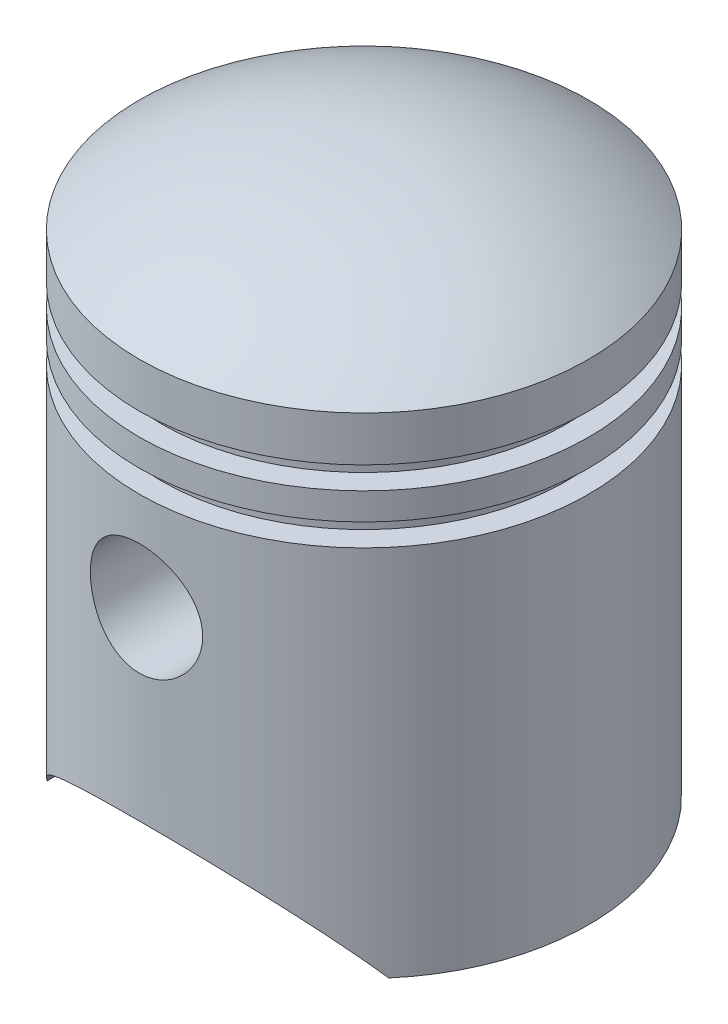
SolidWorks part; units mm, degrees
ref_plane "Front Plane" through (0, 0, 0) normal (0, 0, 1) x (1, 0, 0)
ref_plane "Top Plane" through (0, 0, 0) normal (0, 1, 0) x (1, 0, 0)
ref_plane "Right Plane" through (0, 0, 0) normal (1, 0, 0) x (0, 0, -1)
sketch "Sketch2" plane through (0, 0, 0) normal (0, 0, 1) x (1, 0, 0)
  line L0 (25, 0) -> (25, 41.5)
  line L1 (25, 49.5) -> (22.5, 49.5)
  line L2 (22.5, 49.5) -> (22.5, 47)
  line L3 (22.5, 47) -> (25, 47)
  line L4 (25, 44) -> (22.5, 44)
  line L5 (22.5, 44) -> (22.5, 41.5)
  line L6 (22.5, 41.5) -> (25, 41.5)
  line L7 (25, 49.5) -> (25, 54.5)
  line L8 (25, 44) -> (25, 47)
  line L9 (23, 0) -> (23, 39.5)
  line L10 (20.5, 39.5) -> (23, 39.5)
  line L11 (20.5, 45.5) -> (20.5, 39.5)
  line L12 (20.5, 45.5) -> (20.5, 45.5)
  line L13 (20.5, 45.5) -> (20.5, 45.5)
  line L14 (20.5, 45.5) -> (20.5, 45.5)
  line L15 (20.5, 51.5) -> (20.5, 45.5)
  line L16 (23, 51.5) -> (20.5, 51.5)
  line L17 (23, 51.5) -> (23, 53.4845)
  line L18 (25, 0) -> (23, 0)
  line L19 (0, 62.5) -> (0, 60.4994)
  arc A0 (25, 54.5) -> (0, 62.5) centre (0.9839, 22.5121) ccw
  arc A1 (23, 53.4845) -> (0, 60.4994) centre (0.9839, 22.5121) ccw
  arc A2 (23, 53.4845) -> (0.0492, 60.5006) centre (0.9839, 22.5121) ccw construction
  dimension "D4" = 40
  dimension "D1" = 25
  dimension "D2" = 62.5
  dimension "D3" = 54.5
  dimension "D5" = 5
  dimension "D6" = 2.5
  dimension "D7" = 2.5
  dimension "D8" = 3
  dimension "D9" = 2.5
  dimension "D10" = 2
revolve "Revolve1" add sketch "Sketch2" angle 360 about L19
sketch "Sketch3" plane through (0, 0, 0) normal (0, 0, 1) x (1, 0, 0)
  line L0 (-25, 0) -> (25, 0) construction
  line L1 (0, 30.5) -> (0, 62.5) construction
  line L2 (-19, 0) -> (19, 0)
  circle A0 centre (0, 30.5) radius 6.25
  arc A1 (-19, 0) -> (19, 0) centre (0, -13.05) cw
  point P5 (0, 10)
  dimension "D1" = 12.5
  dimension "D2" = 32
  dimension "D3" = 38
  dimension "D4" = 10
extrude "Cut-Extrude1" cut sketch "Sketch3" against normal through all both and the other way through all
sketch "Sketch4" plane through (0, 0, 0) normal (0, 0, 1) x (1, 0, 0)
  circle A0 centre (0, 30.5) radius 7.25
  circle A1 centre (0, 30.5) radius 6.25
  dimension "D1" = 14.5
  dimension "D2" = 12.5
extrude "Boss-Extrude1" add sketch "Sketch4" along normal up to surface (11.9257 mm away) from offset 12
mirror "Mirror1" about plane through (0, 0, 0) normal (0, 0, 1) of "Boss-Extrude1"
